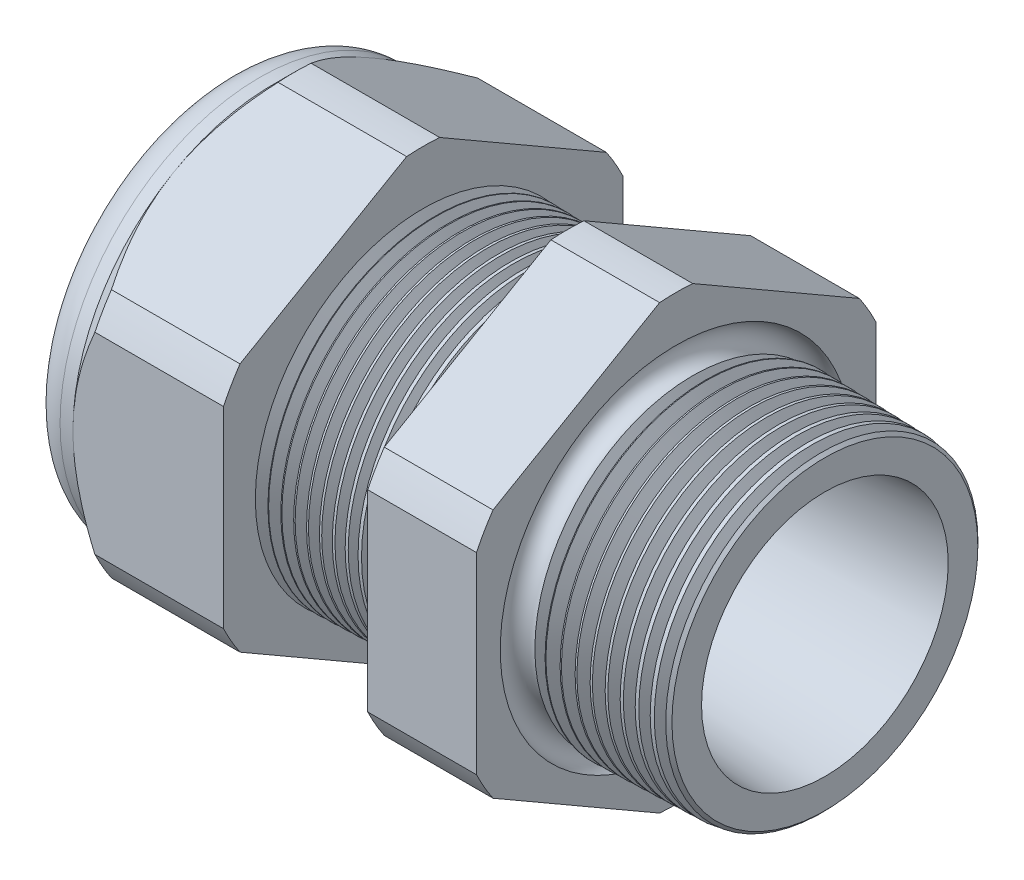
SolidWorks part; units mm, degrees
ref_plane "Front Plane" through (0, 0, 0) normal (0, 0, 1) x (1, 0, 0)
ref_plane "Top Plane" through (0, 0, 0) normal (0, 1, 0) x (1, 0, 0)
ref_plane "Right Plane" through (0, 0, 0) normal (1, 0, 0) x (0, 0, -1)
sketch "Sketch10" plane through (0, 0, 0) normal (0, 0, 1) x (1, 0, 0)
  line L0 (0, 0) -> (-115.3565, 0) construction
  line L1 (-34.798, 5.969) -> (-22.998, 5.969)
  line L2 (1.016, 7.3722) -> (1.016, 9.4042)
  line L3 (-7.874, 9.637) -> (1.016, 9.4042)
  line L4 (-7.874, 23.876) -> (-7.874, 9.637)
  line L5 (-7.874, 23.876) -> (-14.374, 23.876)
  line L6 (-14.374, 23.876) -> (-14.374, 9.8072)
  line L7 (-22.998, 10.033) -> (-14.374, 9.8072)
  line L8 (-22.998, 10.033) -> (-22.998, 23.876)
  line L9 (-22.998, 23.876) -> (-31.998, 23.876)
  line L10 (-31.998, 23.876) -> (-31.998, 11.938)
  line L11 (-31.998, 11.938) -> (-34.798, 11.938)
  line L12 (-34.798, 11.938) -> (-34.798, 5.969)
  line L13 (-22.998, 5.969) -> (1.016, 7.3722)
  dimension "D1" = 35.814
  dimension "D2" = 11.938
  dimension "D3" = 1.5
  dimension "D4" = 2.032
  dimension "A" = 20.066
  dimension "D6" = 23.876
  dimension "D8" = 47.752
  dimension "D9" = 2.8
  dimension "D10" = 9
  dimension "D11" = 6.5
  dimension "D" = 8.89
revolve "Revolve2" add sketch "Sketch10" angle 360 about L0
sketch "Sketch12" plane through (-31.998, 0, 0) normal (-1, 0, 0) x (0, 0, 1)
  line L1 (-0.9882, 13.2143) -> (-10.9498, 7.4629)
  line L2 (-11.938, 5.7513) -> (-11.938, -5.7513)
  line L3 (-10.9498, -7.4629) -> (-0.9882, -13.2143)
  line L4 (0.9882, -13.2143) -> (10.9498, -7.4629)
  line L5 (11.938, -5.7513) -> (11.938, 5.7513)
  line L6 (10.9498, 7.4629) -> (0.9882, 13.2143)
  circle A0 centre (0, 0) radius 11.938 construction
  arc A1 (0.9882, 13.2143) -> (-0.9882, 13.2143) centre (0, 0) ccw
  arc A2 (-10.9498, 7.4629) -> (-11.938, 5.7513) centre (0, 0) ccw
  arc A3 (-11.938, -5.7513) -> (-10.9498, -7.4629) centre (0, 0) ccw
  arc A4 (-0.9882, -13.2143) -> (0.9882, -13.2143) centre (0, 0) ccw
  arc A5 (10.9498, -7.4629) -> (11.938, -5.7513) centre (0, 0) ccw
  arc A6 (11.938, 5.7513) -> (10.9498, 7.4629) centre (0, 0) ccw
  dimension "D2" = 26.5024
  dimension "D1" = 23.876
extrude "Cut-Extrude2" cut sketch "Sketch12" against normal through all flip side to cut
fillet "Fillet4" radius 2.032 1 edges at (-34.798, 0, -11.938)
sketch "Sketch19" plane through (-31.998, 0, 0) normal (-1, 0, 0) x (0, 0, 1)
  line L0 (11.938, 0) -> (11.938, 5.7513) construction
  circle A0 centre (0, 0) radius 11.938
extrude "Cut-Extrude3" cut sketch "Sketch19" against normal blind 2 draft 45 flip side to cut
chamfer "Chamfer1" distance 0.254 angle 45 1 edges at (1.016, 0, -9.4042)
sketch "Sketch21" plane through (-34.798, 0, 0) normal (-1, 0, 0) x (0, 0, 1)
  circle A0 centre (0, 0) radius 5.969
  circle A2 centre (0, 0) radius 5.969 construction
extrude "plug" add sketch "Sketch21" against normal blind 6.35 separate body
sketch "Sketch22" plane through (-34.798, 0, 0) normal (-1, 0, 0) x (0, 0, 1)
  circle A0 centre (0, 0) radius 5.715
  circle A1 centre (0, 0) radius 5.969 construction
  dimension "D1" = 0.254
extrude "Cut-Extrude4" cut sketch "Sketch22" against normal blind 0.508
sketch "Sketch27" plane through (-34.29, 0, 0) normal (-1, 0, 0) x (0, 0, 1)
  line L0 (-4.3624, 0) -> (4.3624, 0) construction
  circle A0 centre (-3.6749, 0) radius 2.032
  circle A1 centre (0, 0) radius 5.715 construction
  dimension "D1" = 0.0081
  dimension "holedia" = 4.064
extrude "plugholes" cut sketch "Sketch27" against normal through all
pattern_circular "CirPattern1" count 3 over 360 about axis through (0, 0, 0) along (1, 0, 0) of "plugholes"
sketch "Sketch28" [suppressed] plane through (-29.464, 0, 0) normal (-1, 0, 0) x (0, 0, 1)
  circle A0 centre (0, 0) radius 0.762
  dimension "midholedia" = 4.064
extrude "midhole" [suppressed] cut sketch "Sketch28" against normal through all
sketch "Sketch29" plane through (0, 0, 0) normal (0, 0, 1) x (1, 0, 0)
  line L0 (-22.998, 10.033) -> (-22.265, 10.0138)
  line L1 (-14.374, 9.8072) -> (-22.998, 10.033) construction
  line L2 (-22.265, 10.0138) -> (-22.6481, 9.3886)
  line L3 (-22.6481, 9.3886) -> (-22.998, 10.033)
  dimension "D1" = 60
  dimension "D2" = 60
  dimension "D3" = 0.635
revolve "Cut-Revolve1" cut sketch "Sketch29" angle 360 about axis through (0, 0, 0) along (-1, 0, 0)
pattern_linear "LPattern1" count 11 spacing 0.762 along (1, 0, 0) of "Cut-Revolve1"
sketch "Sketch30" plane through (0, 0, 0) normal (0, 0, 1) x (1, 0, 0)
  line L0 (-7.874, 9.637) -> (-6.9944, 9.6139)
  line L1 (-7.874, 13.2143) -> (-7.874, 7.4629) construction
  line L2 (0.7621, 9.4108) -> (-7.874, 9.637) construction
  line L3 (-6.9944, 9.6139) -> (-7.4542, 8.8637)
  line L4 (-7.4542, 8.8637) -> (-7.874, 9.637)
  dimension "D1" = 60
  dimension "D2" = 60
  dimension "D3" = 0.762
revolve "Cut-Revolve2" cut sketch "Sketch30" angle 360 about axis through (0, 0, 0) along (-1, 0, 0)
pattern_linear "LPattern2" count 10 spacing 0.889 along (1, 0, 0) of "Cut-Revolve2"
sketch "Sketch31" [suppressed] plane through (-38.354, 0, 0) normal (-1, 0, 0) x (0, 0, 1)
  line L0 (-1.905, 1.905) -> (1.905, 1.905)
  line L1 (-1.905, -1.905) -> (1.905, -1.905)
  circle A0 centre (0, 0) radius 1.905 construction
  arc A1 (-1.905, 1.905) -> (-1.905, -1.905) centre (-1.905, 0) ccw
  arc A2 (1.905, 1.905) -> (1.905, -1.905) centre (1.905, 0) cw
extrude "Cut-Extrude5" [suppressed] cut sketch "Sketch31" against normal through all
sketch "Sketch32" plane through (0, 0, 0) normal (0, 0, 1) x (1, 0, 0)
  line L0 (-7.874, 13.2143) -> (-7.874, 7.4629) construction
  circle A0 centre (-7.747, 9.637) radius 0.889
  dimension "D2" = 1.778
  dimension "D1" = 0.127
revolve "Cut-Revolve3" cut sketch "Sketch32" angle 360 about axis through (0, 0, 0) along (-1, 0, 0)
